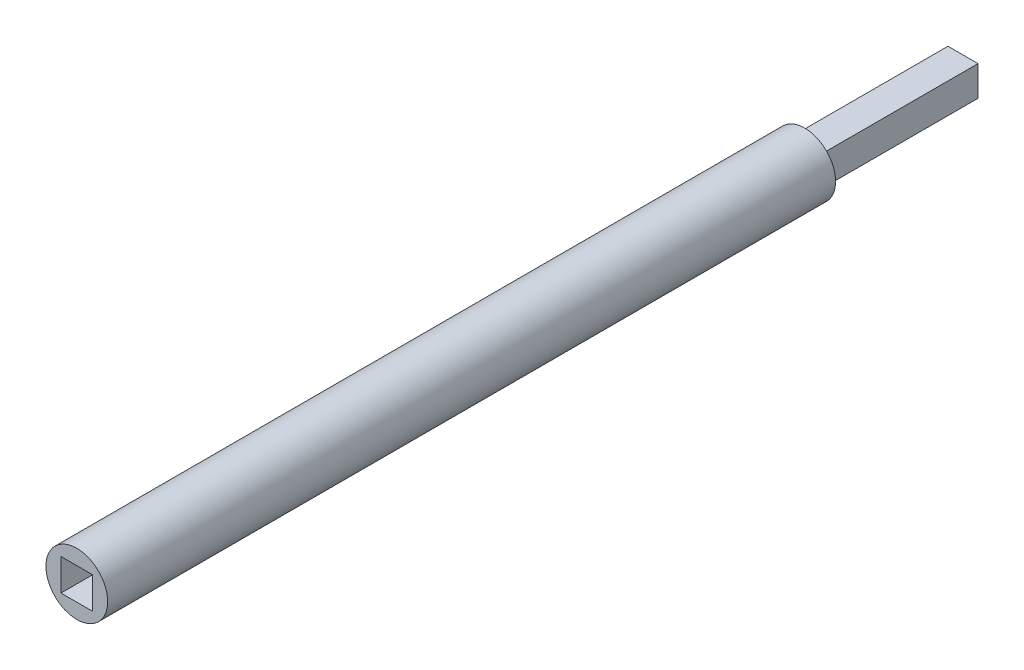
SolidWorks part; units mm, degrees
ref_plane "Front Plane" through (0, 0, 0) normal (0, 0, 1) x (1, 0, 0)
ref_plane "Top Plane" through (0, 0, 0) normal (0, 1, 0) x (1, 0, 0)
ref_plane "Right Plane" through (0, 0, 0) normal (1, 0, 0) x (0, 0, -1)
sketch "Sketch1" plane through (0, 0, 0) normal (0, 0, 1) x (1, 0, 0)
  circle A0 centre (0, 0) radius 0.975
  dimension "D1" = 1.95
extrude "Boss-Extrude1" add sketch "Sketch1" along normal blind 23
sketch "Sketch2" plane through (0, 0, 0) normal (0, 0, -1) x (-1, 0, 0)
  line L1 (-0.475, 0.475) -> (0.475, 0.475)
  line L2 (-0.475, 0.475) -> (-0.475, -0.475)
  line L3 (-0.475, -0.475) -> (0.475, -0.475)
  line L4 (0.475, 0.475) -> (0.475, -0.475)
  line L5 (-0.475, 0.475) -> (0.475, -0.475) construction
  line L6 (-0.475, -0.475) -> (0.475, 0.475) construction
  point P0 (0, 0)
  dimension "D1" = 0.95
extrude "Boss-Extrude2" add sketch "Sketch2" along normal blind 5
sketch "Sketch3" plane through (0, 0, 23) normal (0, 0, 1) x (1, 0, 0)
  line L1 (-0.5, 0.5) -> (0.5, 0.5)
  line L2 (-0.5, 0.5) -> (-0.5, -0.5)
  line L3 (-0.5, -0.5) -> (0.5, -0.5)
  line L4 (0.5, 0.5) -> (0.5, -0.5)
  line L5 (-0.5, 0.5) -> (0.5, -0.5) construction
  line L6 (-0.5, -0.5) -> (0.5, 0.5) construction
  point P0 (0, 0)
  dimension "D1" = 1
extrude "Cut-Extrude1" cut sketch "Sketch3" against normal blind 5
